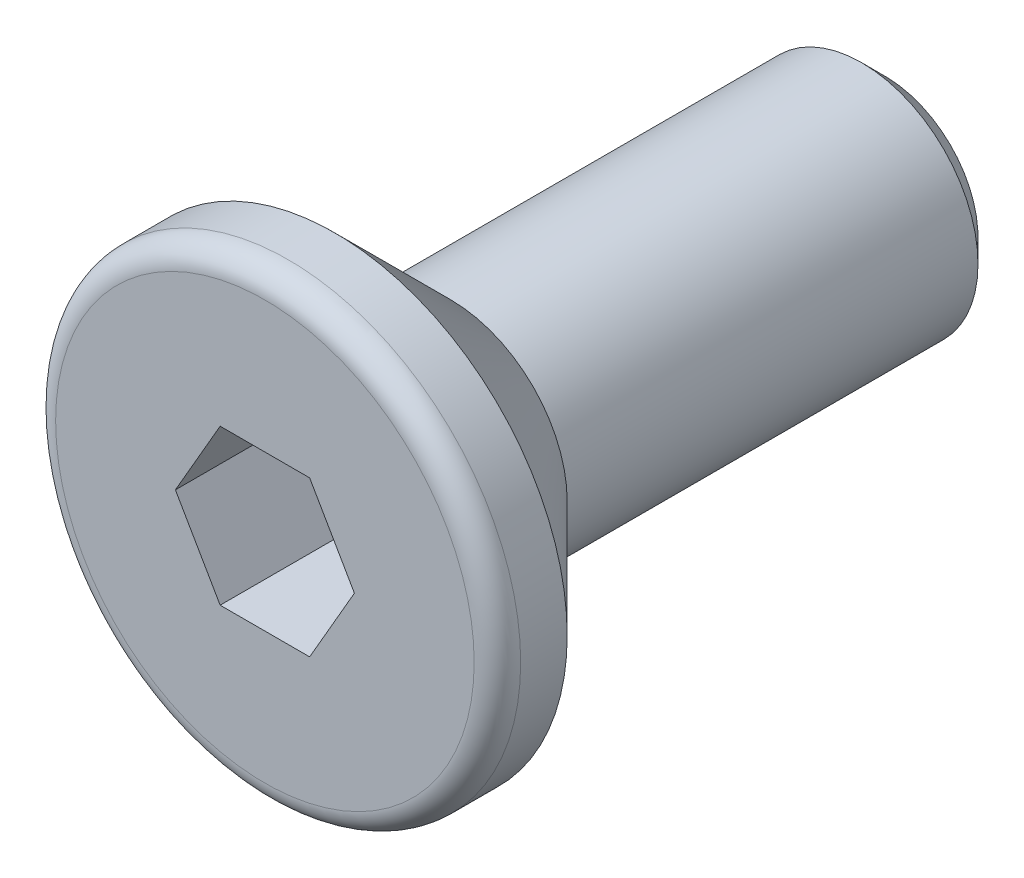
SolidWorks part; units mm, degrees
ref_plane "前视基准面" through (0, 0, 0) normal (0, 0, 1) x (1, 0, 0)
ref_plane "上视基准面" through (0, 0, 0) normal (0, 1, 0) x (1, 0, 0)
ref_plane "右视基准面" through (0, 0, 0) normal (1, 0, 0) x (0, 0, -1)
sketch "草图1" plane through (0, 0, 0) normal (1, 0, 0) x (0, 0, -1)
  line L0 (-4, 0) -> (-4, 3)
  line L1 (-4, 3) -> (-3.1, 3)
  line L2 (-3.1, 3) -> (-1.6, 1.5)
  line L3 (-1.6, 1.5) -> (3.7, 1.5)
  line L4 (3.7, 1.5) -> (4, 1.2)
  line L5 (4, 1.2) -> (4, 0)
  line L6 (4, 0) -> (-4, 0)
  point P2 (-2.2188, 2.8472)
  dimension "D1" = 8
  dimension "D2" = 3
  dimension "D3" = 45
  dimension "D4" = 0.3
  dimension "D5" = 2.4
  dimension "D6" = 1.5
revolve "旋转1" add sketch "草图1" angle 360 about L6
sketch "草图2" plane through (0, 0, 4) normal (0, 0, 1) x (1, 0, 0)
  line L1 (1.1547, 0) -> (0.5774, 1)
  line L2 (0.5774, 1) -> (-0.5774, 1)
  line L3 (-0.5774, 1) -> (-1.1547, 0)
  line L4 (-1.1547, 0) -> (-0.5774, -1)
  line L5 (-0.5774, -1) -> (0.5774, -1)
  line L6 (0.5774, -1) -> (1.1547, 0)
  circle A0 centre (0, 0) radius 1 construction
  dimension "D1" = 2
extrude "切除-拉伸1" cut sketch "草图2" against normal blind 1.5
fillet "圆角1" radius 0.3 1 edges at (-3, 0, 4)
